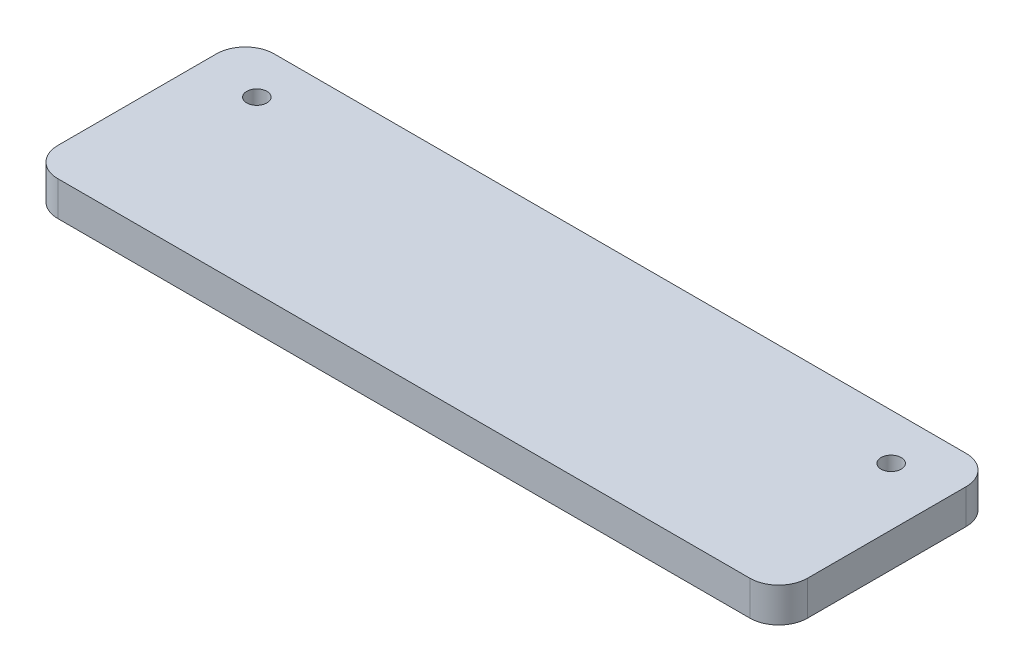
SolidWorks part; units mm, degrees
ref_plane "Front Plane" through (0, 0, 0) normal (0, 0, 1) x (1, 0, 0)
ref_plane "Top Plane" through (0, 0, 0) normal (0, 1, 0) x (1, 0, 0)
ref_plane "Right Plane" through (0, 0, 0) normal (1, 0, 0) x (0, 0, -1)
sketch "Sketch1" plane through (0, 0, 0) normal (0, 1, 0) x (1, 0, 0)
  line L1 (0, 0) -> (130, 0)
  line L2 (0, 0) -> (0, 37.5)
  line L3 (0, 37.5) -> (130, 37.5)
  line L4 (130, 0) -> (130, 37.5)
  dimension "D1" = 130
  dimension "D2" = 37.5
extrude "Boss-Extrude1" add sketch "Sketch1" along normal blind 6
fillet "Fillet1" radius 5 4 edges at (0, 3, -37.5) (130, 3, -37.5) (130, 3, 0) (0, 3, 0)
sketch "Sketch2" plane through (0, 6, 0) normal (0, 1, 0) x (1, 0, 0)
  line L0 (125, 37.5) -> (5, 37.5) construction
  line L1 (0, 32.5) -> (0, 5) construction
  line L2 (130, 5) -> (130, 32.5) construction
  circle A0 centre (10, 29.5) radius 1.75
  circle A1 centre (120, 29.5) radius 1.75
  point P4 (0, 0)
  dimension "D1" = 3.5
  dimension "D2" = 3.5
  dimension "D3" = 8
  dimension "D4" = 10
  dimension "D5" = 10
extrude "Cut-Extrude1" cut sketch "Sketch2" against normal blind 6
